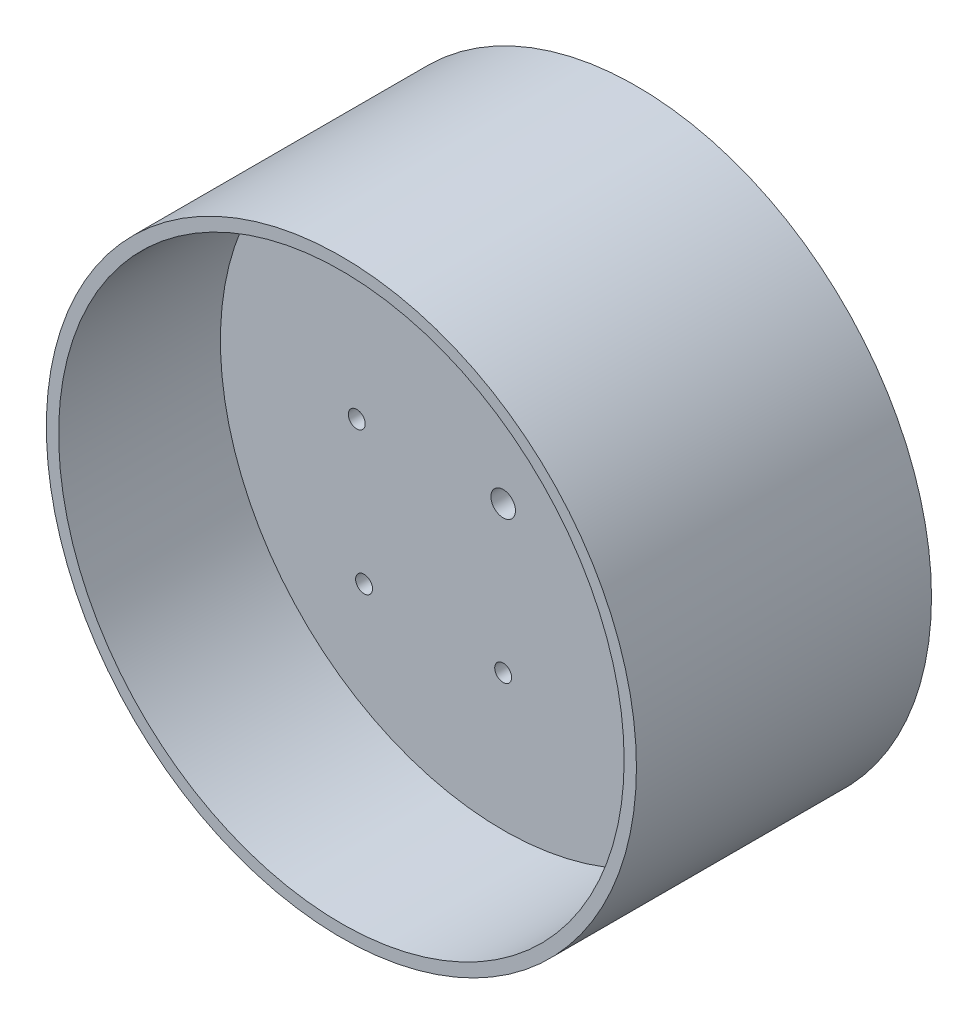
SolidWorks part; units mm, degrees
material "6061 Alloy"
ref_plane "Front Plane" through (0, 0, 0) normal (0, 0, 1) x (1, 0, 0)
ref_plane "Top Plane" through (0, 0, 0) normal (0, 1, 0) x (1, 0, 0)
ref_plane "Right Plane" through (0, 0, 0) normal (1, 0, 0) x (0, 0, -1)
sketch "Sketch1" plane through (0, 0, 0) normal (0, 0, 1) x (1, 0, 0)
  circle A0 centre (0, 0) radius 76.2
  circle A1 centre (0, 0) radius 73.025
  dimension "D1" = 152.4
  dimension "D2" = 146.05
extrude "Boss-Extrude1" add sketch "Sketch1" along normal blind 76.2
sketch "Sketch3" plane through (0, 0, 0) normal (0, 0, 1) x (1, 0, 0)
  circle A0 centre (0, 0) radius 76.2
extrude "Boss-Extrude2" add sketch "Sketch3" along normal blind 34.417
sketch "Sketch4" plane through (0, 0, 34.417) normal (0, 0, 1) x (1, 0, 0)
  line L1 (-31.75, 31.75) -> (31.75, 31.75)
  line L2 (-31.75, 31.75) -> (-31.75, -31.75)
  line L3 (-31.75, -31.75) -> (31.75, -31.75)
  line L4 (31.75, 31.75) -> (31.75, -31.75)
  point P5 (0, 31.75)
  point P7 (-31.75, 0)
  dimension "D1" = 63.5
  dimension "2.5" = 63.5
extrude "Cut-Extrude1" [suppressed] cut sketch "Sketch4" against normal blind 1.27
sketch "Sketch5" plane through (0, 0, 34.417) normal (0, 0, 1) x (1, 0, 0)
  line L5 (-25.4, -25.4) -> (25.4, -25.4) construction
  line L6 (-25.4, -25.4) -> (-25.4, 25.4) construction
  line L7 (-25.4, 25.4) -> (25.4, 25.4) construction
  line L8 (25.4, -25.4) -> (25.4, 25.4) construction
  circle A0 centre (0, 37.813) radius 2.1828
  circle A1 centre (37.813, 0) radius 2.1828
  circle A2 centre (-37.813, 0) radius 2.1828
  circle A3 centre (0, -37.813) radius 2.1828
  point P20 (0, -25.4)
  point P21 (25.4, 0)
  dimension "D1" = 4.3656
  dimension "D2" = 4.3656
  dimension "D3" = 4.3656
  dimension "D4" = 4.3656
  dimension "D5" = 12.413
  dimension "D6" = 12.413
  dimension "D7" = 12.413
  dimension "D8" = 12.413
  dimension "D9" = 50.8
  dimension "D10" = 50.8
extrude "Cut-Extrude2" cut sketch "Sketch5" against normal through all contours L6 L5 L8 L7 | A1 | A0 | A2 | A3
sketch "Sketch10" plane through (0, 0, 76.2) normal (0, 0, 1) x (1, 0, 0)
  line L1 (71.6254, -14.2286) -> (73.6429, -1.5885)
  line L2 (73.6429, -1.5885) -> (72.1723, 11.1269)
  line L3 (72.1723, 11.1269) -> (69.745, 23.6947)
  line L4 (69.745, 23.6947) -> (64.0142, 35.1402)
  line L5 (64.0142, 35.1402) -> (57.4348, 46.1199)
  line L6 (57.4348, 46.1199) -> (48.135, 54.9151)
  line L7 (48.135, 54.9151) -> (38.1971, 62.9824)
  line L8 (38.1971, 62.9824) -> (26.45, 68.0665)
  line L9 (26.45, 68.0665) -> (14.3523, 72.2482)
  line L10 (14.3523, 72.2482) -> (1.5748, 73.008)
  line L11 (1.5748, 73.008) -> (-11.2236, 72.7999)
  line L12 (-11.2236, 72.7999) -> (-23.4904, 69.1437)
  line L16 (-23.4904, 69.1437) -> (-35.4458, 64.5708)
  line L17 (-35.4458, 64.5708) -> (-45.7223, 56.9396)
  line L18 (-45.7223, 56.9396) -> (-55.3927, 48.5536)
  line L19 (-55.3927, 48.5536) -> (-62.4394, 37.8678)
  line L20 (-62.4394, 37.8678) -> (-68.6584, 26.68)
  line L21 (-68.6584, 26.68) -> (-71.6254, 14.2286)
  line L22 (-71.6254, 14.2286) -> (-73.6429, 1.5885)
  line L23 (-73.6429, 1.5885) -> (-72.1723, -11.1269)
  line L24 (-72.1723, -11.1269) -> (-69.745, -23.6947)
  line L25 (-69.745, -23.6947) -> (-72.1723, -11.1269)
  line L26 (-72.1723, -11.1269) -> (-69.745, -23.6947)
  line L27 (-69.745, -23.6947) -> (-64.0142, -35.1402)
  line L28 (-64.0142, -35.1402) -> (-57.4348, -46.1199)
  line L29 (-57.4348, -46.1199) -> (-48.135, -54.9151)
  line L30 (-48.135, -54.9151) -> (-38.1971, -62.9824)
  line L31 (-38.1971, -62.9824) -> (-26.45, -68.0665)
  line L32 (-26.45, -68.0665) -> (-14.3523, -72.2482)
  line L33 (-14.3523, -72.2482) -> (-1.5748, -73.008)
  line L34 (-1.5748, -73.008) -> (11.2236, -72.7999)
  line L35 (11.2236, -72.7999) -> (23.4904, -69.1437)
  line L36 (23.4904, -69.1437) -> (35.4458, -64.5708)
  line L37 (35.4458, -64.5708) -> (45.7223, -56.9396)
  line L38 (45.7223, -56.9396) -> (55.3927, -48.5536)
  line L39 (55.3927, -48.5536) -> (62.4394, -37.8678)
  line L40 (62.4394, -37.8678) -> (68.6584, -26.68)
  line L41 (68.6584, -26.68) -> (71.6254, -14.2286)
  circle A7 centre (0, 0) radius 73.66 construction
  circle A8 centre (0, 0) radius 73.025 construction
  circle A9 centre (0, 0) radius 73.025 construction
  circle M41 centre (0, 0) radius 73.025
  dimension "D1" = 147.32
extrude "Cut-Extrude10" [suppressed] cut sketch "Sketch10" against normal up to surface (69.85 mm away) contours M41 | L20 L21 M41 | L18 L19 M41 | L16 L17 M41 | L11 L12 M41 | L9 L10 M41 | L7 L8 M41 | L5 L6 M41 | L3 L4 M41 | L1 L2 M41 | L40 L41 M41 | L38 L39 M41 | L36 L37 M41 | L34 L35 M41 | L32 L33 M41 | L30 L31 M41 | L28 L29 M41 | L24 L27 M41 | L22 L23 M41
fillet "Fillet1" [suppressed] radius 9.525
sketch "Sketch11" plane through (0, 0, 34.417) normal (0, 0, 1) x (1, 0, 0)
  line L0 (-71.842, 0) -> (0, 71.842) construction
  line L1 (0, 71.842) -> (71.842, 0) construction
  line L2 (71.842, 0) -> (0, -71.842) construction
  line L3 (0, -71.842) -> (-71.842, 0) construction
  line L4 (0, -37.813) -> (37.813, 0) construction
  circle A0 centre (-35.921, 35.921) radius 2.1828
  circle A1 centre (-35.921, -35.921) radius 2.1828
  circle A2 centre (35.921, -35.921) radius 2.1828
  circle A3 centre (35.921, 35.921) radius 2.1828
  dimension "D5" = 90
  dimension "D6" = 4.3656
  dimension "D7" = 4.3656
  dimension "D8" = 4.3656
  dimension "D9" = 4.3656
  dimension "D1" = 101.6
  dimension "D2" = 101.6
  dimension "D3" = 50.8
  dimension "D4" = 50.8
extrude "Cut-Extrude11" cut sketch "Sketch11" against normal through all
sketch "Sketch12" plane through (0, 0, 34.417) normal (0, 0, 1) x (1, 0, 0)
  circle A0 centre (0, 0) radius 3.175
  dimension "D1" = 6.35
extrude "Cut-Extrude12" cut sketch "Sketch12" against normal through all
